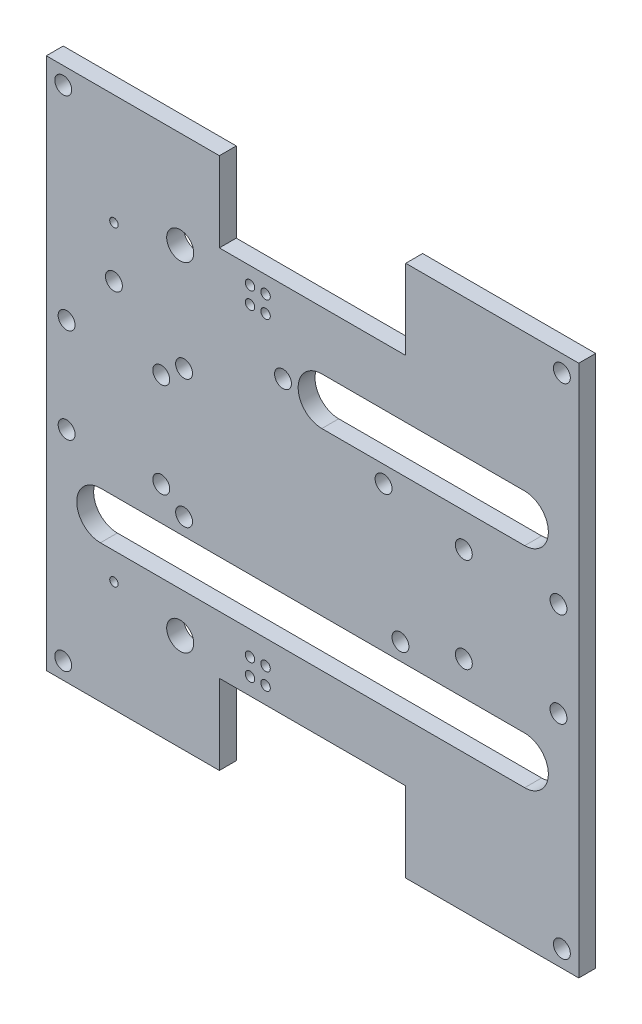
SolidWorks part; units mm, degrees
ref_plane "Front Plane" through (0, 0, 0) normal (0, 0, 1) x (1, 0, 0)
ref_plane "Top Plane" through (0, 0, 0) normal (0, 1, 0) x (1, 0, 0)
ref_plane "Right Plane" through (0, 0, 0) normal (1, 0, 0) x (0, 0, -1)
sketch "Sketch1" plane through (0, 0, 0) normal (0, 0, 1) x (1, 0, 0)
  line L5 (122.4099, 37.5406) -> (157.9699, 73.1006) construction
  line L6 (346.701, 12.7177) -> (504.181, 12.7177) construction
  line L11 (214.7899, 125.3206) -> (214.7899, -14.6794) construction
  line L12 (307.1699, 37.5406) -> (304.9248, 39.7856) construction
  line L16 (273.8549, 70.8555) -> (271.6099, 73.1006) construction
  line L17 (197.1369, -8.3294) -> (191.2949, -1.9794) construction
  line L22 (135.1099, 15.9506) -> (294.4699, 15.9506) construction
  line L23 (135.1099, 24.8406) -> (294.4699, 24.8406)
  line L28 (135.1099, 7.0606) -> (294.4699, 7.0606)
  line L29 (218.2699, 94.6906) -> (294.4699, 94.6906) construction
  line L30 (346.701, 12.7177) -> (346.701, -43.1623) construction
  line L31 (346.701, -43.1623) -> (504.181, -43.1623) construction
  line L32 (504.181, 12.7177) -> (504.181, -43.1623) construction
  line L33 (151.2899, 81.9906) -> (252.8899, 81.9906) construction
  line L34 (151.2899, 81.9906) -> (151.2899, 28.6506) construction
  line L35 (151.2899, 28.6506) -> (252.8899, 28.6506) construction
  line L36 (252.8899, 81.9906) -> (252.8899, 28.6506) construction
  line L37 (249.7899, 155.3206) -> (314.7899, 155.3206)
  line L38 (114.7899, 155.3206) -> (179.7899, 155.3206)
  line L39 (114.7899, 155.3206) -> (114.7899, -44.6794)
  line L40 (114.7899, -44.6794) -> (179.7899, -44.6794)
  line L41 (314.7899, 155.3206) -> (314.7899, -44.6794)
  line L43 (179.7899, 155.3206) -> (179.7899, 125.3206)
  line L44 (179.7899, 125.3206) -> (249.7899, 125.3206)
  line L45 (249.7899, 155.3206) -> (249.7899, 125.3206)
  line L46 (114.7899, 55.3206) -> (314.7899, 55.3206) construction
  line L47 (249.7899, -44.6794) -> (249.7899, -14.6794)
  line L48 (179.7899, -14.6794) -> (249.7899, -14.6794)
  line L49 (179.7899, -44.6794) -> (179.7899, -14.6794)
  line L50 (249.7899, -44.6794) -> (314.7899, -44.6794)
  line L51 (218.2699, 103.5806) -> (294.4699, 103.5806)
  line L52 (218.2699, 85.8006) -> (294.4699, 85.8006)
  circle A1 centre (140.1899, -3.0994) radius 1.5875
  circle A2 centre (122.4099, 73.1006) radius 3.175
  circle A3 centre (122.4099, 37.5406) radius 3.175
  circle A4 centre (157.9699, 37.5406) radius 3.175
  circle A5 centre (140.1899, 113.7406) radius 1.5875
  circle A6 centre (157.9699, 73.1006) radius 3.175
  circle A9 centre (271.6099, 73.1006) radius 3.175
  circle A10 centre (307.1699, 73.1006) radius 3.175
  circle A11 centre (271.6099, 37.5406) radius 3.175
  circle A12 centre (307.1699, 37.5406) radius 3.175
  circle A13 centre (121.1399, 148.9706) radius 3.175
  circle A14 centre (140.1899, 94.6772) radius 3.175
  circle A15 centre (203.6899, 94.6772) radius 3.175
  circle A16 centre (191.2949, -1.9794) radius 1.778
  circle A17 centre (197.1369, -1.9794) radius 1.778
  circle A18 centre (191.2949, -8.3294) radius 1.778
  circle A19 centre (197.1369, -8.3294) radius 1.778
  circle A20 centre (191.2949, 118.9706) radius 1.778
  circle A21 centre (191.2949, 112.6206) radius 1.778
  circle A22 centre (197.1369, 112.6206) radius 1.778
  circle A23 centre (197.1369, 118.9706) radius 1.778
  circle A24 centre (166.5299, 79.4506) radius 3.175
  circle A25 centre (241.4599, 79.4506) radius 3.175
  circle A26 centre (166.5299, 31.1906) radius 3.175
  circle A27 centre (247.8099, 31.1906) radius 3.175
  circle A28 centre (121.1399, -38.3294) radius 3.175
  circle A29 centre (308.4399, -38.3294) radius 3.175
  circle A30 centre (308.4399, 148.9706) radius 3.175
  arc A31 (135.1099, 24.8406) -> (135.1099, 7.0606) centre (135.1099, 15.9506) ccw
  arc A32 (294.4699, 7.0606) -> (294.4699, 24.8406) centre (294.4699, 15.9506) ccw
  arc A33 (218.2699, 103.5806) -> (218.2699, 85.8006) centre (218.2699, 94.6906) ccw
  arc A34 (294.4699, 85.8006) -> (294.4699, 103.5806) centre (294.4699, 94.6906) ccw
  circle A35 centre (165.0767, 118.8206) radius 5.08
  circle A36 centre (165.0767, -8.1794) radius 5.08
  point P0 (0, 0)
  point P1 (140.1899, 55.3206)
  point P31 (194.2159, -5.1544)
  point P36 (214.7899, 15.9506)
  point P93 (0, 0)
  point P94 (256.3699, 94.6906)
  point P101 (0, 0)
  point P106 (0, 0)
  dimension "D12" = 25.4
  dimension "D13" = 25.4
  dimension "D19" = 35.56
  dimension "D26" = 6.35
  dimension "D27" = 6.35
  dimension "D30" = 6.35
  dimension "D14" = 6.35
  dimension "D17" = 6.35
  dimension "D18" = 6.35
  dimension "D33" = 3.556
  dimension "D34" = 5.842
  dimension "D39" = 6.35
  dimension "D44" = 6.35
  dimension "D48" = 6.35
  dimension "D49" = 6.35
  dimension "D50" = 8.89
  dimension "D55" = 8.89
  dimension "D58" = 10.16
  dimension "D4" = 58.42
  dimension "D5" = 17.78
  dimension "D8" = 157.48
  dimension "D9" = 55.88
  dimension "D10" = 101.6
  dimension "D11" = 53.34
  dimension "D15" = 6.35
  dimension "D16" = 6.35
  dimension "D20" = 200
  dimension "D21" = 200
  dimension "D22" = 30
  dimension "D23" = 70
  dimension "D24" = 65
  dimension "D25" = 0
  dimension "D28" = 35.56
  dimension "D29" = 0
  dimension "D6" = 0
  dimension "D7" = 0
  dimension "D31" = 63.5
  dimension "D32" = 25.4
  dimension "D35" = 6.35
  dimension "D36" = 6.35
  dimension "D37" = 20.574
  dimension "D38" = 6.35
  dimension "D40" = 26.67
  dimension "D41" = 63.5
  dimension "D42" = 2.54
  dimension "D43" = 15.24
  dimension "D45" = 74.93
  dimension "D46" = 81.28
  dimension "D47" = 0
  dimension "D51" = 39.37
  dimension "D52" = 20.32
  dimension "D53" = 20.32
  dimension "D54" = 39.37
  dimension "D56" = 20.32
  dimension "D57" = 76.2
  dimension "D59" = 25.4
  dimension "D60" = 63.5
extrude "Boss-Extrude1" add sketch "Sketch1" along normal blind 6.35
